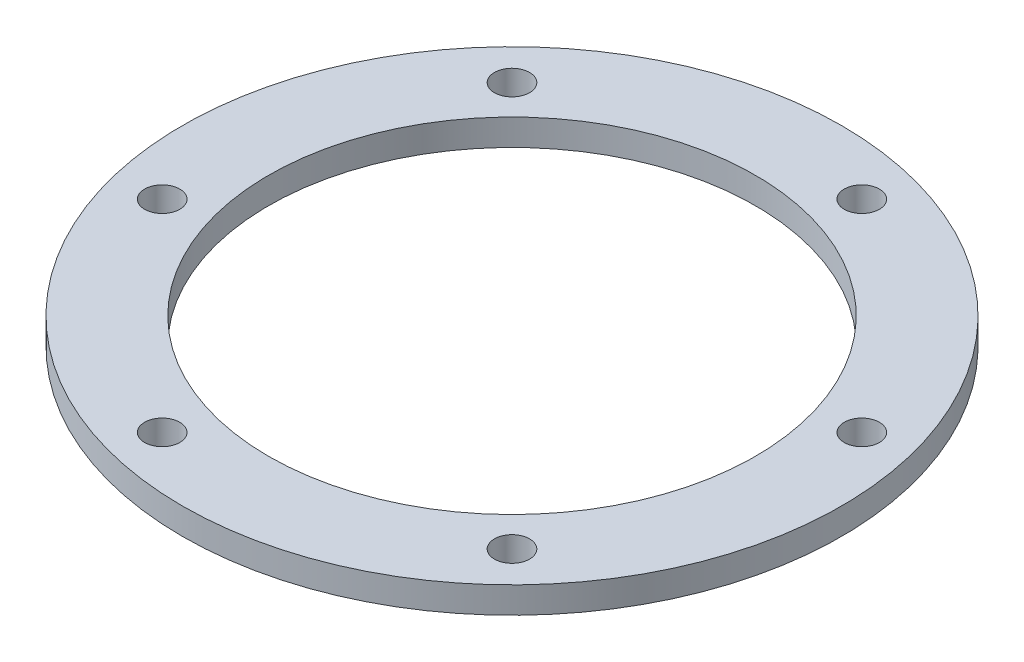
SolidWorks part; units mm, degrees
material "Acrylic (Medium-high impact)"
ref_plane "Front Plane" through (0, 0, 0) normal (0, 0, 1) x (1, 0, 0)
ref_plane "Top Plane" through (0, 0, 0) normal (0, 1, 0) x (1, 0, 0)
ref_plane "Right Plane" through (0, 0, 0) normal (1, 0, 0) x (0, 0, -1)
sketch "Sketch1" plane through (0, 0, 0) normal (0, 1, 0) x (1, 0, 0)
  line L0 (0, 0) -> (32.5, 0) construction
  line L2 (22.981, -22.981) -> (0, 0) construction
  circle A0 centre (0, 0) radius 37.5
  circle A1 centre (0, 0) radius 27.7
  circle A2 centre (0, 0) radius 32.5 construction
  circle A3 centre (22.981, -22.981) radius 2
  circle A10 centre (-8.4116, -31.3926) radius 2
  circle A11 centre (-31.3926, -8.4116) radius 2
  circle A12 centre (-22.981, 22.981) radius 2
  circle A13 centre (8.4116, 31.3926) radius 2
  circle A14 centre (31.3926, 8.4116) radius 2
  point P18 (0, 0)
  point P22 (0, 0)
  dimension "D1" = 75
  dimension "D2" = 55.4
  dimension "D3" = 65
  dimension "D5" = 4
  dimension "D4" = 45
  dimension "D6" = 6
extrude "Boss-Extrude1" add sketch "Sketch1" along normal blind 3
